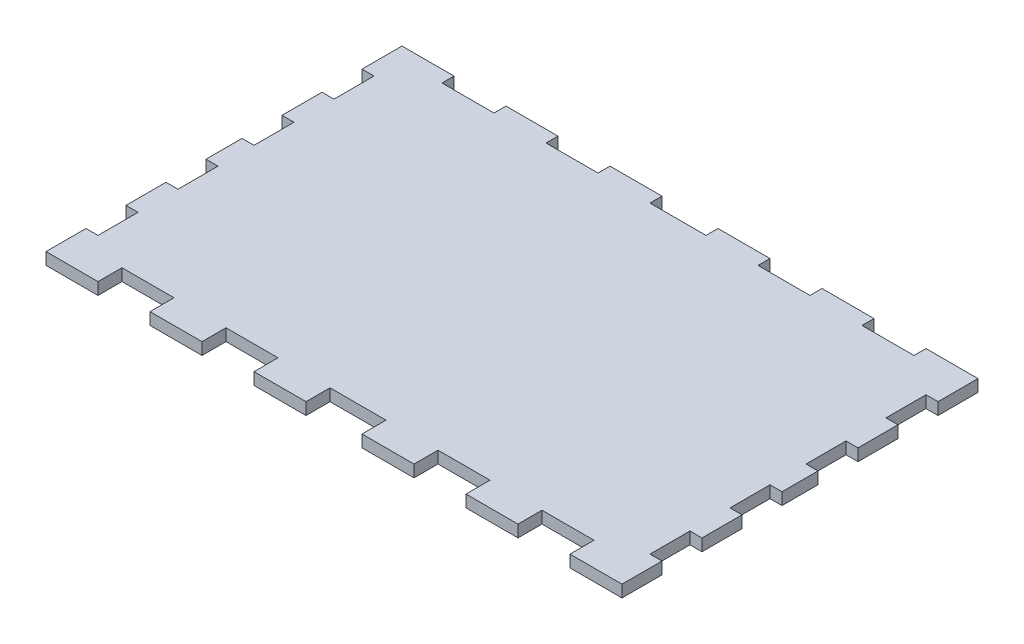
SolidWorks part; units mm, degrees
ref_plane "Front Plane" through (0, 0, 0) normal (0, 0, 1) x (1, 0, 0)
ref_plane "Top Plane" through (0, 0, 0) normal (0, 1, 0) x (1, 0, 0)
ref_plane "Right Plane" through (0, 0, 0) normal (1, 0, 0) x (0, 0, -1)
sketch "Sketch1" plane through (0, 0, 0) normal (0, 1, 0) x (1, 0, 0)
  line L0 (26, 89) -> (39, 89)
  line L1 (0, 0) -> (13, 0)
  line L2 (0, 0) -> (0, 10)
  line L3 (0, 89) -> (13, 89)
  line L4 (144, 0) -> (144, 10)
  line L5 (0, 79) -> (0, 89)
  line L6 (13, 0) -> (13, 6)
  line L7 (13, 6) -> (26, 6)
  line L8 (26, 0) -> (26, 6)
  line L9 (144, 79) -> (141, 79)
  line L10 (39, 0) -> (39, 6)
  line L11 (39, 6) -> (52, 6)
  line L12 (52, 0) -> (52, 6)
  line L14 (65, 0) -> (65, 6)
  line L15 (65, 6) -> (79, 6)
  line L16 (79, 0) -> (79, 6)
  line L17 (144, 69) -> (141, 69)
  line L18 (92, 0) -> (92, 6)
  line L19 (92, 6) -> (105, 6)
  line L20 (105, 0) -> (105, 6)
  line L21 (141, 79) -> (141, 69)
  line L22 (118, 0) -> (118, 6)
  line L23 (118, 6) -> (131, 6)
  line L24 (131, 0) -> (131, 6)
  line L25 (52, 0) -> (65, 0)
  line L26 (13, 89) -> (13, 86)
  line L27 (13, 86) -> (26, 86)
  line L28 (26, 89) -> (26, 86)
  line L29 (79, 0) -> (92, 0)
  line L30 (39, 89) -> (39, 86)
  line L31 (39, 86) -> (52, 86)
  line L32 (52, 89) -> (52, 86)
  line L33 (105, 0) -> (118, 0)
  line L34 (65, 89) -> (65, 86)
  line L35 (65, 86) -> (79, 86)
  line L36 (79, 89) -> (79, 86)
  line L37 (131, 0) -> (144, 0)
  line L38 (92, 89) -> (92, 86)
  line L39 (92, 86) -> (105, 86)
  line L40 (105, 89) -> (105, 86)
  line L41 (144, 59) -> (141, 59)
  line L42 (118, 89) -> (118, 86)
  line L43 (118, 86) -> (131, 86)
  line L44 (131, 89) -> (131, 86)
  line L45 (52, 89) -> (65, 89)
  line L46 (79, 89) -> (92, 89)
  line L47 (105, 89) -> (118, 89)
  line L48 (131, 89) -> (144, 89)
  line L49 (26, 0) -> (39, 0)
  line L51 (144, 49) -> (141, 49)
  line L52 (141, 59) -> (141, 49)
  line L53 (144, 40) -> (141, 40)
  line L55 (144, 30) -> (141, 30)
  line L56 (141, 40) -> (141, 30)
  line L57 (144, 20) -> (141, 20)
  line L59 (144, 10) -> (141, 10)
  line L60 (141, 20) -> (141, 10)
  line L61 (0, 79) -> (3, 79)
  line L62 (144, 59) -> (144, 69)
  line L63 (0, 69) -> (3, 69)
  line L64 (3, 79) -> (3, 69)
  line L65 (0, 59) -> (3, 59)
  line L66 (144, 40) -> (144, 49)
  line L67 (0, 49) -> (3, 49)
  line L68 (3, 59) -> (3, 49)
  line L69 (0, 40) -> (3, 40)
  line L70 (144, 20) -> (144, 30)
  line L71 (0, 30) -> (3, 30)
  line L72 (3, 40) -> (3, 30)
  line L73 (0, 20) -> (3, 20)
  line L75 (0, 10) -> (3, 10)
  line L76 (3, 20) -> (3, 10)
  line L77 (0, 59) -> (0, 69)
  line L78 (0, 40) -> (0, 49)
  line L79 (0, 20) -> (0, 30)
  line L80 (144, 79) -> (144, 89)
  dimension "D1" = 144
  dimension "D2" = 89
  dimension "D3" = 13
  dimension "D4" = 13
  dimension "D5" = 13
  dimension "D6" = 13
  dimension "D7" = 13
  dimension "D8" = 14
  dimension "D9" = 13
  dimension "D10" = 13
  dimension "D11" = 13
  dimension "D12" = 13
  dimension "D13" = 6
  dimension "D14" = 14
  dimension "D15" = 13
  dimension "D16" = 13
  dimension "D17" = 13
  dimension "D18" = 13
  dimension "D19" = 13
  dimension "D20" = 13
  dimension "D21" = 13
  dimension "D22" = 13
  dimension "D23" = 13
  dimension "D24" = 3
  dimension "D25" = 9
  dimension "D26" = 10
  dimension "D27" = 10
  dimension "D28" = 10
  dimension "D29" = 10
  dimension "D30" = 10
  dimension "D31" = 10
  dimension "D32" = 10
  dimension "D33" = 3
  dimension "D34" = 9
  dimension "D35" = 10
  dimension "D36" = 10
  dimension "D37" = 10
  dimension "D38" = 10
  dimension "D39" = 10
  dimension "D40" = 10
  dimension "D41" = 10
  dimension "D42" = 3
extrude "Boss-Extrude1" add sketch "Sketch1" along normal blind 3
